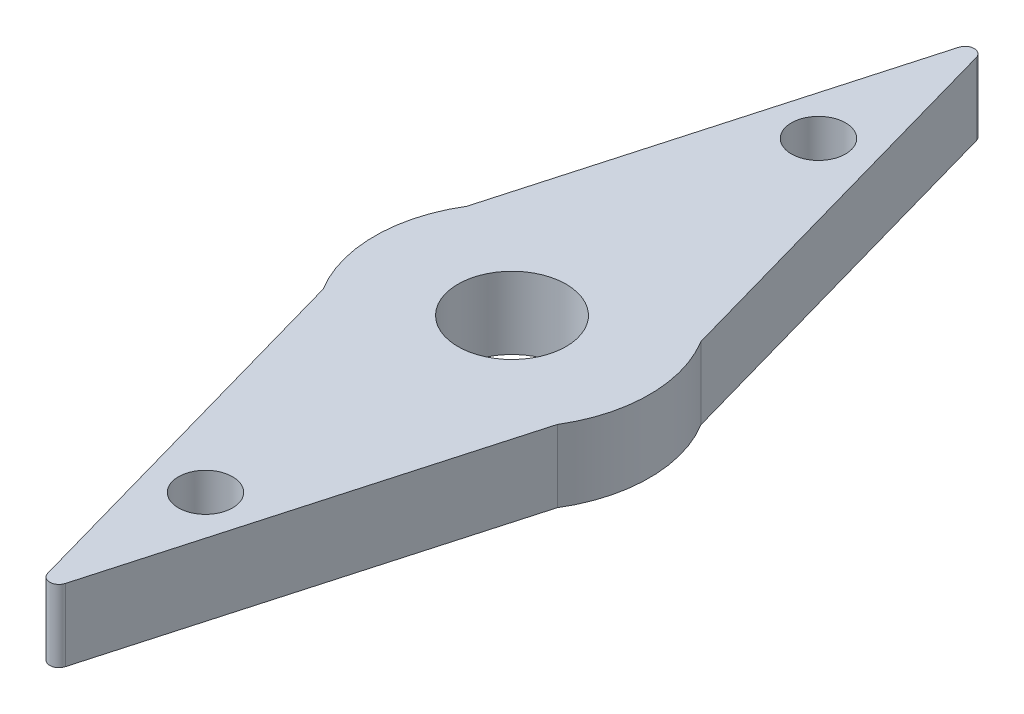
SolidWorks part; units mm, degrees
ref_plane "Front Plane" through (0, 0, 0) normal (0, 0, 1) x (1, 0, 0)
ref_plane "Top Plane" through (0, 0, 0) normal (0, 1, 0) x (1, 0, 0)
ref_plane "Right Plane" through (0, 0, 0) normal (1, 0, 0) x (0, 0, -1)
sketch "Sketch1" plane through (0, 0, 0) normal (0, 1, 0) x (1, 0, 0)
  circle A0 centre (0, 0) radius 3.81
  dimension "D1" = 7.62
extrude "Boss-Extrude1" add sketch "Sketch1" along normal blind 2
sketch "Sketch2" plane through (0, 2, 0) normal (0, 1, 0) x (1, 0, 0)
  line L0 (-3.81, 0) -> (3.81, 0) construction
  line L1 (3.81, 0) -> (0, 13.5)
  line L2 (0, 13.5) -> (-3.81, 0)
  line L3 (0, -13.5) -> (-3.81, 0)
  line L4 (3.81, 0) -> (0, -13.5)
  line L5 (-3.81, 0) -> (3.81, 0)
  circle A0 centre (0, 0) radius 3.81 construction
  circle M2 centre (0, 0) radius 3.81
  dimension "D1" = 27
extrude "Boss-Extrude2" add sketch "Sketch2" against normal up to surface (2 mm away) contours L4 L3 M2 | L1 L2 M2 up to face at (0, 0, 3.81)
fillet "Fillet1" radius 0.254 2 edges at (0, 1, 13.5) (0, 1, -13.5)
sketch "Sketch3" plane through (0, 2, 0) normal (0, 1, 0) x (1, 0, 0)
  line L0 (0, 12.8188) -> (0, -12.8188) construction
  line L1 (-3.81, 0) -> (3.81, 0) construction
  arc A0 (0.2445, 12.6338) -> (-0.2445, 12.6338) centre (0, 12.5648) ccw construction
  arc A1 (-0.2445, -12.6338) -> (0.2445, -12.6338) centre (0, -12.5648) ccw construction
  arc A2 (-3.2478, 1.9919) -> (-3.2478, -1.9919) centre (0, 0) ccw construction
  arc A3 (3.2478, -1.9919) -> (3.2478, 1.9919) centre (0, 0) ccw construction
  circle A4 centre (0, 8.5) radius 0.75
  circle A5 centre (0, -8.5) radius 0.75
  dimension "D1" = 8.5
  dimension "D2" = 1.5
extrude "Cut-Extrude1" cut sketch "Sketch3" against normal up to surface (2 mm away) up to face at (0, 0, 0)
sketch "Sketch4" plane through (0, 0, 0) normal (0, -1, 0) x (1, 0, 0)
  circle A0 centre (0, 0) radius 1.5
  dimension "D1" = 3
extrude "Cut-Extrude2" cut sketch "Sketch4" against normal through all
